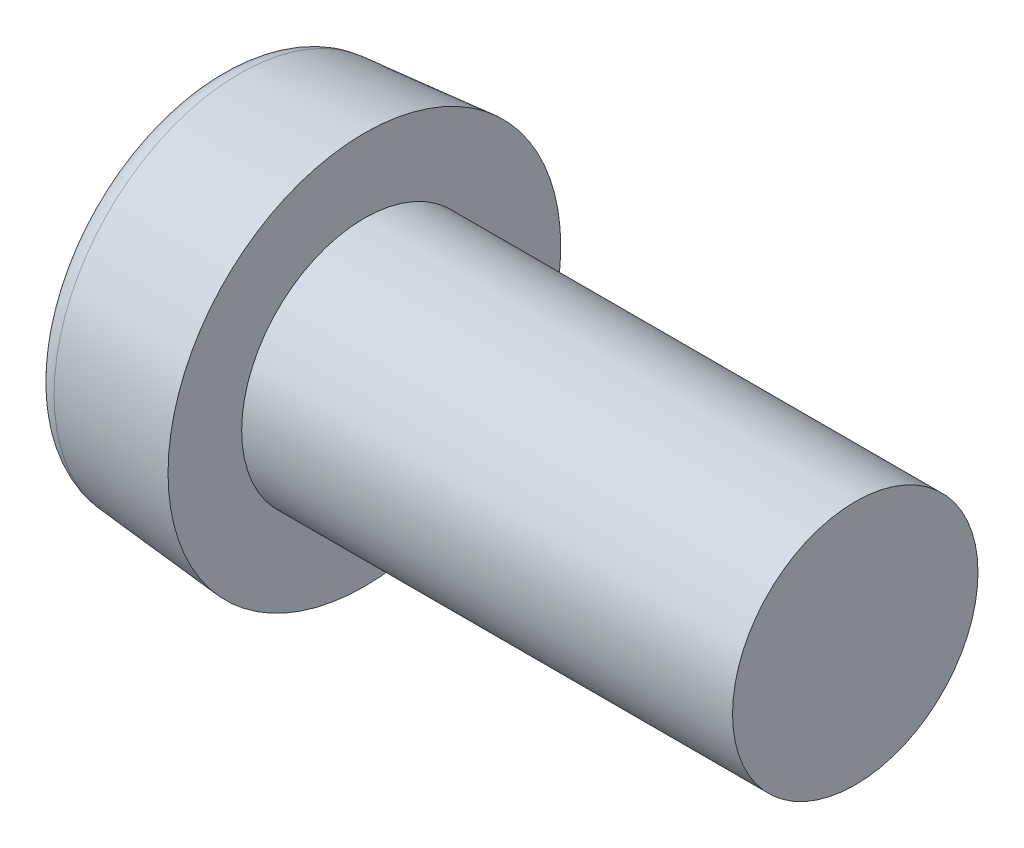
SolidWorks part; units mm, degrees
ref_plane "Front" through (0, 0, 0) normal (0, 0, 1) x (1, 0, 0)
ref_plane "Top" through (0, 0, 0) normal (0, 1, 0) x (1, 0, 0)
ref_plane "Right" through (0, 0, 0) normal (1, 0, 0) x (0, 0, -1)
ref_plane "Plane1" through (6, 0, 0) normal (1, 0, 0) x (0, 0, -1)
sketch "Sketch1" plane through (6, 0, 0) normal (1, 0, 0) x (0, 0, -1)
  circle A0 centre (0, 0) radius 8
  dimension "dk" = 16
extrude "BaseHead" add sketch "Sketch1" against normal blind 6 draft 5
sketch "Sketch2" plane through (6, 0, 0) normal (1, 0, 0) x (0, 0, -1)
  circle A0 centre (0, 0) radius 3
sketch "Sketch8" plane through (0, 0, 0) normal (0, 0, 1) x (1, 0, 0)
  line L0 (0, 0) -> (35.73, 0) construction
  line L1 (7.1525, 0) -> (7.1525, -2) construction
  line L2 (6, -8) -> (6, 8) construction
  line L3 (11.6578, 0) -> (11.6578, -9.026) construction
  line L4 (6, 5) -> (26, 5)
  line L5 (26, 5) -> (26, 0)
  line L7 (26, 0) -> (6, 0)
  line L9 (6, 5) -> (6, 0)
  arc A0 (6.7996, -0.1884) -> (7.126, -0.3991) centre (7.1525, 0) ccw construction
  dimension "r" = 0.4
  dimension "a" = 2
  dimension "d" = 10
  dimension "D4" = 9.026
  dimension "l" = 20
revolve "Revolve1" add sketch "Sketch8" angle 360 about L0
cosmetic thread "ThreadCosmetic1" [suppressed] parameters "bb"=20, "THD_MINOR"=8.376
sketch "Sketch4" plane through (0, 0, 0) normal (1, 0, 0) x (0, 0, -1)
  line L1 (0, 3.8221) -> (-3.31, 1.911) construction
  line L2 (-3.31, 1.911) -> (-3.31, -1.911) construction
  line L3 (-3.31, -1.911) -> (0, -3.8221) construction
  line L4 (0, -3.8221) -> (3.31, -1.911) construction
  line L5 (3.31, -1.911) -> (3.31, 1.911) construction
  line L6 (3.31, 1.911) -> (0, 3.8221) construction
  line L7 (1.655, 2.8665) -> (-1.655, 2.8665) construction
  line L8 (-1.655, 2.8665) -> (-3.31, 0) construction
  line L9 (-3.31, 0) -> (-1.655, -2.8665) construction
  line L10 (-1.655, -2.8665) -> (1.655, -2.8665) construction
  line L11 (1.655, -2.8665) -> (3.31, 0) construction
  line L12 (3.31, 0) -> (1.655, 2.8665) construction
  circle A0 centre (0, 0) radius 3.8221 construction
  circle A1 centre (0, 0) radius 3.31 construction
  spline S0 degree 3 poles (0, 4.4101) (1.5277, 2.646) (3.8192, 2.205) (3.0554, 0) (3.8192, -2.205) (1.5277, -2.646) (0, -4.4101) (-1.5277, -2.646) (-3.8192, -2.205) (-3.0554, 0) (-3.8192, 2.205) (-1.5277, 2.646) (0, 4.4101) (1.5277, 2.646) (3.8192, 2.205) knots -0.25 -0.166667 -0.083333 0 0.083333 0.166667 0.25 0.333333 0.416667 0.5 0.583333 0.666667 0.75 0.833333 0.916667 1 1.083333 1.166667 1.25 only from (1.655, 2.8665) to (1.655, 2.8665)
  dimension "B" = 6.62
extrude "Socket" cut sketch "Sketch4" along normal blind 3
sketch "Sketch5" plane through (3, 0, 0) normal (-1, 0, 0) x (0, 0, 1)
  spline S1 degree 3 poles (0, 4.4101) (-1.5277, 2.646) (-3.8192, 2.205) (-3.0554, 0) (-3.8192, -2.205) (-1.5277, -2.646) (0, -4.4101) (1.5277, -2.646) (3.8192, -2.205) (3.0554, 0) (3.8192, 2.205) (1.5277, 2.646) (0, 4.4101) (-1.5277, 2.646) (-3.8192, 2.205) knots -0.25 -0.166667 -0.083333 0 0.083333 0.166667 0.25 0.333333 0.416667 0.5 0.583333 0.666667 0.75 0.833333 0.916667 1 1.083333 1.166667 1.25 only from (-1.655, 2.8665) to (-1.655, 2.8665)
  spline S2 degree 3 poles (0, 4.4101) (-1.5277, 2.646) (-3.8192, 2.205) (-3.0554, 0) (-3.8192, -2.205) (-1.5277, -2.646) (0, -4.4101) (1.5277, -2.646) (3.8192, -2.205) (3.0554, 0) (3.8192, 2.205) (1.5277, 2.646) (0, 4.4101) (-1.5277, 2.646) (-3.8192, 2.205) knots -0.25 -0.166667 -0.083333 0 0.083333 0.166667 0.25 0.333333 0.416667 0.5 0.583333 0.666667 0.75 0.833333 0.916667 1 1.083333 1.166667 1.25 only from (-1.655, 2.8665) to (-1.655, 2.8665)
  dimension "D1" = 0
ref_plane "Plane2" through (4, 0, 0) normal (-1, 0, 0) x (0, 0, 1)
sketch "Sketch7" plane through (4, 0, 0) normal (-1, 0, 0) x (0, 0, 1)
  point P0 (0, 0)
loft "Cut-Loft1" cut profiles "Sketch7", "Sketch5"
sketch "Sketch6" plane through (-30.7487, 13.2487, 0) normal (0, 0, 1) x (0, -1, 0)
  line L0 (13.2487, 89.8637) -> (13.2487, 24.8312) construction
  line L1 (-5.9393, 36.7487) -> (8.9607, 36.7487)
  line L2 (-5.9393, 36.7487) -> (-5.9393, 18.7487)
  line L3 (-5.9393, 18.7487) -> (8.2487, 18.7487)
  line L4 (9.0607, 36.8487) -> (9.0607, 14.9487)
  line L5 (18.2487, 56.7487) -> (8.2487, 56.7487) construction
  line L6 (8.2487, 18.7487) -> (9.0607, 14.9487)
  line L9 (21.2487, 36.7487) -> (5.2487, 36.7487) construction
  arc A0 (8.9607, 36.7487) -> (9.0607, 36.8487) centre (8.9607, 36.8487) ccw
  dimension "d1" = 8.376
  dimension "D2" = 15
  dimension "b" = 38
  dimension "D3" = 10
  dimension "x" = 3.8
fillet "HeadFillet2" radius 1 1 edges at (0, 0, -7.4751)
sketch "Sketch9" plane through (0, 0, 0) normal (0, 0, 1) x (1, 0, 0)
  line L0 (26, 4.2968) -> (26.406, 5)
  line L1 (26.406, 5) -> (26.406, 5.812)
  line L2 (26.406, 5.812) -> (25.594, 5.812)
  line L3 (25.594, 5.812) -> (25.594, 5)
  line L4 (25.594, 5) -> (26, 4.2968)
  line L5 (26, -5) -> (26, 5) construction
  line L6 (0, 0) -> (28.2938, 0) construction
  line L7 (0, 6.5587) -> (0, -6.5587) construction
  dimension "D1" = 0.812
  dimension "D2" = 10
revolve "Cut-Revolve10" [suppressed] cut sketch "Sketch9" angle 360 about L6
pattern_linear "LPattern10" [suppressed] count 21 spacing 0.9744 along (1, 0, 0)
equation "\"D1@Plane1\"=\"k@BaseHead\""
equation "\"D1@Plane2\" = \"t@Socket\" / 3"
equation "\"D2@Sketch9\" =\"d@Sketch8\""
equation "\"D1@Sketch9\" =  ( \"d@Sketch8\" - \"THD_MINOR@ThreadCosmetic1\" )  / 2"
equation "\"D3@LPattern10\" = \"D1@Sketch9\" * 1.2"
equation "\"D1@LPattern10\" = \"bb@ThreadCosmetic1\" / \"D3@LPattern10\" "
equation "\"D3@Sketch6\" = \"d@Sketch8\""
